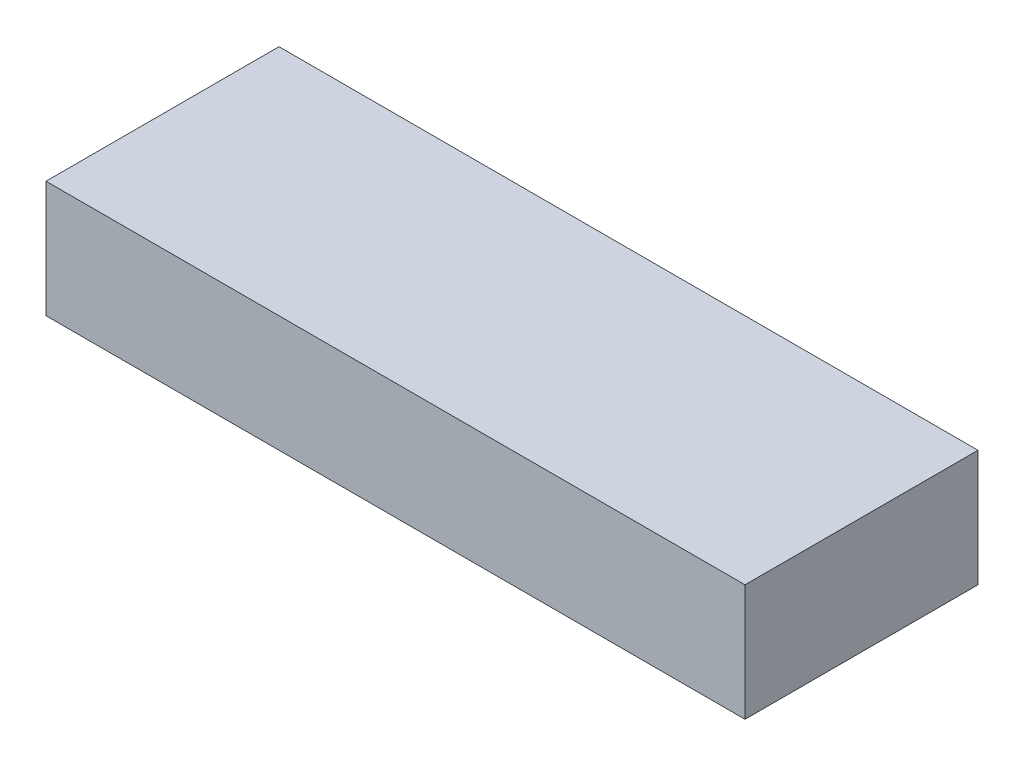
SolidWorks part; units mm, degrees
material "Acrylic (Medium-high impact)"
ref_plane "Front Plane" through (0, 0, 0) normal (0, 0, 1) x (1, 0, 0)
ref_plane "Top Plane" through (0, 0, 0) normal (0, 1, 0) x (1, 0, 0)
ref_plane "Right Plane" through (0, 0, 0) normal (1, 0, 0) x (0, 0, -1)
sketch "Sketch1" plane through (0, 0, 0) normal (0, 1, 0) x (1, 0, 0)
  line L1 (-19.05, -6.35) -> (19.05, -6.35)
  line L2 (-19.05, -6.35) -> (-19.05, 6.35)
  line L3 (-19.05, 6.35) -> (19.05, 6.35)
  line L4 (19.05, -6.35) -> (19.05, 6.35)
  line L5 (-19.05, -6.35) -> (19.05, 6.35) construction
  line L6 (-19.05, 6.35) -> (19.05, -6.35) construction
  point P0 (0, 0)
extrude "Boss-Extrude1" add sketch "Sketch1" along normal blind 6.35
sketch "Sketch2" plane through (0, 6.35, 0) normal (0, 1, 0) x (1, 0, 0)
  text T0 "<b>BATTERY</b>" font "Century Gothic" height in points 16
extrude "Boss-Extrude2" add sketch "Sketch2" against normal blind 0.508 separate body
